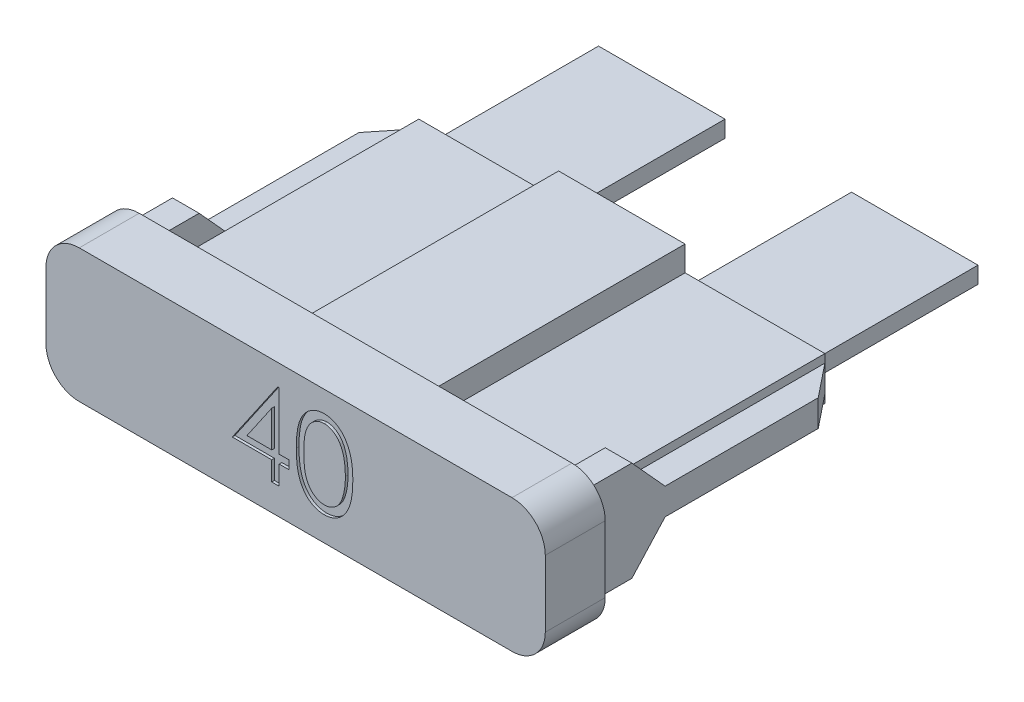
SolidWorks part; units mm, degrees
ref_plane "Front Plane" through (0, 0, 0) normal (0, 0, 1) x (1, 0, 0)
ref_plane "Top Plane" through (0, 0, 0) normal (0, 1, 0) x (1, 0, 0)
ref_plane "Right Plane" through (0, 0, 0) normal (1, 0, 0) x (0, 0, -1)
sketch "Sketch1" plane through (0, 0, 0) normal (0, 0, 1) x (1, 0, 0)
  line L1 (1.27, 0) -> (17.78, 0)
  line L2 (0, 1.27) -> (0, 3.81)
  line L3 (1.27, 5.08) -> (17.78, 5.08)
  line L4 (19.05, 1.27) -> (19.05, 3.81)
  arc A0 (0, 3.81) -> (1.27, 5.08) centre (1.27, 3.81) cw
  arc A1 (1.27, 0) -> (0, 1.27) centre (1.27, 1.27) cw
  arc A2 (19.05, 1.27) -> (17.78, 0) centre (17.78, 1.27) cw
  arc A3 (17.78, 5.08) -> (19.05, 3.81) centre (17.78, 3.81) cw
  point P8 (0, 0)
  dimension "D3" = 1.27
  dimension "D1" = 5.08
  dimension "D2" = 19.05
extrude "Extrude1" add sketch "Sketch1" along normal blind 2.286
sketch "Sketch2" plane through (0, 0, 0) normal (0, 0, -1) x (-1, 0, 0)
  line L0 (-7.62, 2.2225) -> (-7.62, 1.27)
  line L1 (-16.764, 2.8575) -> (-11.43, 2.8575)
  line L2 (-16.764, 2.8575) -> (-16.764, 2.2225)
  line L3 (-16.764, 2.2225) -> (-11.43, 2.2225)
  line L4 (-11.43, 2.2225) -> (-11.43, 1.27)
  line L5 (-11.43, 3.81) -> (-7.62, 3.81)
  line L6 (-11.43, 3.81) -> (-11.43, 2.8575)
  line L7 (-11.43, 1.27) -> (-7.62, 1.27)
  line L8 (-7.62, 3.81) -> (-7.62, 2.8575)
  line L9 (-7.62, 2.8575) -> (-2.286, 2.8575)
  line L10 (-11.938, 4.318) -> (-11.938, 3.3655)
  line L11 (-7.62, 2.2225) -> (-2.286, 2.2225)
  line L12 (-2.286, 2.8575) -> (-2.286, 2.2225)
  line L13 (-17.272, 3.3655) -> (-11.938, 3.3655)
  line L14 (-17.272, 3.3655) -> (-17.272, 1.7145)
  line L15 (-17.272, 1.7145) -> (-11.938, 1.7145)
  line L16 (-11.938, 1.7145) -> (-11.938, 0.762)
  line L17 (-11.938, 0.762) -> (-7.112, 0.762)
  line L18 (-7.112, 1.7145) -> (-7.112, 0.762)
  line L19 (-7.112, 1.7145) -> (-1.778, 1.7145)
  line L20 (-1.778, 3.3655) -> (-1.778, 1.7145)
  line L21 (-7.112, 3.3655) -> (-1.778, 3.3655)
  line L22 (-7.112, 4.318) -> (-7.112, 3.3655)
  line L23 (-11.938, 4.318) -> (-7.112, 4.318)
  line L24 (-17.78, 5.08) -> (-1.27, 5.08) construction
  line L25 (-1.27, 0) -> (-17.78, 0) construction
  line L26 (-19.05, 1.27) -> (-19.05, 3.81) construction
  line L27 (0, 3.81) -> (0, 1.27) construction
  dimension "D1" = 0.635
  dimension "D2" = 2.54
  dimension "D3" = 0.9525
  dimension "D5" = 0.762
  dimension "D6" = 0.762
  dimension "D7" = 1.778
  dimension "D8" = 14.478
  dimension "D9" = 3.81
  dimension "D10" = 5.334
  dimension "D11" = 5.334
  dimension "D12" = 1.778
  dimension "D4" = 0.508
extrude "Extrude2" add sketch "Sketch2" along normal blind 10.16
sketch "Sketch3" plane through (1.778, 0, 0) normal (-1, 0, 0) x (0, 0, 1)
  line L0 (-10.16, 1.7145) -> (-10.16, 3.3655) construction
  line L1 (-10.16, 3.048) -> (-3.048, 3.048)
  line L2 (-10.16, 3.048) -> (-10.16, 2.032)
  line L3 (-10.16, 2.032) -> (-3.048, 2.032)
  line L5 (0, 3.81) -> (0, 1.27) construction
  line L6 (-1.778, 4.445) -> (0, 4.445)
  line L8 (-1.778, 0.635) -> (0, 0.635)
  line L9 (0, 4.445) -> (0, 0.635)
  line L10 (-10.16, 3.3655) -> (0, 3.3655) construction
  line L11 (-10.16, 1.7145) -> (0, 1.7145) construction
  line L12 (-1.778, 4.445) -> (-3.048, 3.048)
  line L13 (-3.048, 2.032) -> (-1.778, 0.635)
  dimension "D1" = 1.016
  dimension "D2" = 0.3175
  dimension "D3" = 0.3175
  dimension "D4" = 3.81
  dimension "D5" = 1.397
  dimension "D6" = 1.397
  dimension "D7" = 1.27
  dimension "D8" = 1.778
extrude "Extrude3" add sketch "Sketch3" along normal blind 1.016
sketch "Sketch4" plane through (17.272, 0, 0) normal (1, 0, 0) x (0, 0, -1)
  line L0 (10.16, 3.3655) -> (10.16, 1.7145) construction
  line L1 (3.048, 3.048) -> (10.16, 3.048)
  line L3 (3.048, 2.032) -> (10.16, 2.032)
  line L4 (10.16, 3.048) -> (10.16, 2.032)
  line L5 (0, 3.81) -> (0, 5.08) construction
  line L6 (0, 4.445) -> (1.778, 4.445)
  line L7 (0, 4.445) -> (0, 0.635)
  line L8 (0, 0.635) -> (1.778, 0.635)
  line L10 (1.778, 4.445) -> (3.048, 3.048)
  line L11 (1.778, 0.635) -> (3.048, 2.032)
  line L12 (10.16, 3.3655) -> (0, 3.3655) construction
  dimension "D1" = 1.016
  dimension "D2" = 0.3175
  dimension "D3" = 1.397
  dimension "D4" = 3.81
  dimension "D5" = 1.27
  dimension "D6" = 7.112
extrude "Extrude4" add sketch "Sketch4" along normal blind 1.016
chamfer "Chamfer1" distance 1.016 distance2 1.27 2 edges at (0.762, 2.54, -10.16) (18.288, 2.54, -10.16)
sketch "Sketch8" plane through (0, 2.2225, 0) normal (0, 1, 0) x (-1, 0, 0)
  line L0 (-11.938, -10.16) -> (-11.938, 0) construction
  line L1 (-2.286, 0) -> (-7.112, 0)
  line L2 (-2.286, 0) -> (-2.286, -16.51)
  line L3 (-2.286, -16.51) -> (-7.112, -16.51)
  line L4 (-7.112, 0) -> (-7.112, -6.858)
  line L5 (-16.764, 0) -> (-11.938, 0)
  line L6 (-16.764, 0) -> (-16.764, -16.51)
  line L7 (-16.764, -16.51) -> (-11.938, -16.51)
  line L8 (-11.938, 0) -> (-11.938, -6.858)
  line L9 (-7.112, -10.16) -> (-7.112, 0) construction
  line L10 (-1.778, -10.16) -> (-7.112, -10.16) construction
  line L11 (-11.938, -10.16) -> (-17.272, -10.16) construction
  line L12 (-7.112, -7.62) -> (-8.128, -7.62)
  line L13 (-8.763, -6.985) -> (-8.763, -3.175)
  line L14 (-9.398, -2.54) -> (-9.652, -2.54)
  line L15 (-10.287, -3.175) -> (-10.287, -6.985)
  line L16 (-10.922, -7.62) -> (-11.938, -7.62)
  line L17 (-7.112, -10.16) -> (-11.938, -10.16) construction
  line L18 (-11.684, -6.858) -> (-11.938, -6.858)
  line L19 (-11.049, -3.175) -> (-11.049, -6.223)
  line L20 (-9.398, -1.778) -> (-9.652, -1.778)
  line L21 (-8.001, -6.223) -> (-8.001, -3.175)
  line L22 (-7.112, -6.858) -> (-7.366, -6.858)
  line L23 (-11.938, -7.62) -> (-11.938, -16.51)
  line L24 (-7.112, -7.62) -> (-7.112, -16.51)
  arc A0 (-9.652, -2.54) -> (-10.287, -3.175) centre (-9.652, -3.175) ccw
  arc A1 (-8.763, -3.175) -> (-9.398, -2.54) centre (-9.398, -3.175) ccw
  arc A2 (-10.922, -7.62) -> (-10.287, -6.985) centre (-10.922, -6.985) ccw
  arc A3 (-8.128, -7.62) -> (-8.763, -6.985) centre (-8.128, -6.985) cw
  arc A4 (-9.652, -1.778) -> (-11.049, -3.175) centre (-9.652, -3.175) ccw
  arc A5 (-8.001, -3.175) -> (-9.398, -1.778) centre (-9.398, -3.175) ccw
  arc A6 (-7.366, -6.858) -> (-8.001, -6.223) centre (-7.366, -6.223) cw
  arc A7 (-11.684, -6.858) -> (-11.049, -6.223) centre (-11.684, -6.223) ccw
  point P26 (-10.287, -2.54)
  point P29 (-8.763, -2.54)
  point P32 (-10.287, -7.62)
  point P35 (-8.763, -7.62)
  dimension "D6" = 0.635
  dimension "D8" = 0.635
  dimension "D1" = 6.35
  dimension "D2" = 6.35
  dimension "D3" = 1.524
  dimension "D4" = 5.08
  dimension "D5" = 2.54
  dimension "D7" = 0.762
extrude "Blade" add sketch "Sketch8" along normal up to surface (0.635 mm away) up to face at (4.953, 2.8575, -5.08)
sketch "Sketch5" plane through (0, 0, 2.286) normal (0, 0, 1) x (1, 0, 0)
  line L0 (0, 3.81) -> (0, 1.27) construction
  line L1 (1.27, 0) -> (17.78, 0) construction
  text T0 "10" font "Century Gothic" height in points 12
  dimension "D1" = 6.7818
  dimension "D2" = 0.9525
extrude "\"10\"" [suppressed] cut sketch "Sketch5" against normal blind 0.1016
sketch "Sketch6" plane through (0, 0, 2.286) normal (0, 0, 1) x (1, 0, 0)
  line L0 (1.27, 0) -> (17.78, 0) construction
  line L1 (0, 3.81) -> (0, 1.27) construction
  text T0 "40" font "Century Gothic" height in points 12
  dimension "D1" = 1.016
  dimension "D2" = 6.985
extrude "\"40\"" cut sketch "Sketch6" against normal blind 0.1016
sketch "Sketch7" [suppressed] plane through (0, 0, 2.286) normal (0, 0, 1) x (1, 0, 0)
  line L0 (1.27, 0) -> (17.78, 0) construction
  line L1 (0, 3.81) -> (0, 1.27) construction
  text T0 "30" font "Century Gothic" height in points 12
  dimension "D1" = 1.016
  dimension "D2" = 6.985
extrude "\"30\"" [suppressed] cut sketch "Sketch7" against normal blind 0.1016
sketch "Sketch9" [suppressed] plane through (0, 0, 2.286) normal (0, 0, 1) x (1, 0, 0)
  line L0 (1.27, 0) -> (17.78, 0) construction
  line L1 (0, 3.81) -> (0, 1.27) construction
  text T0 "7.5" font "Century Gothic" height in points 12
  dimension "D1" = 1.016
  dimension "D2" = 6.604
extrude "\"7.5\"" [suppressed] cut sketch "Sketch9" against normal blind 0.1016
sketch "Sketch10" [suppressed] plane through (0, 0, 2.286) normal (0, 0, 1) x (1, 0, 0)
  line L0 (1.27, 0) -> (17.78, 0) construction
  line L1 (0, 3.81) -> (0, 1.27) construction
  text T0 "1" font "Century Gothic" height in points 12
  dimension "D1" = 1.016
  dimension "D2" = 8.255
extrude "\"1\"" [suppressed] cut sketch "Sketch10" against normal blind 0.1016
sketch "Sketch11" [suppressed] plane through (0, 0, 2.286) normal (0, 0, 1) x (1, 0, 0)
  line L0 (1.27, 0) -> (17.78, 0) construction
  line L1 (0, 3.81) -> (0, 1.27) construction
  text T0 "15" font "Century Gothic" height in points 12
  dimension "D1" = 1.016
  dimension "D2" = 6.858
extrude "\"15\"" [suppressed] cut sketch "Sketch11" against normal blind 0.1016
sketch "Sketch12" [suppressed] plane through (0, 0, 2.286) normal (0, 0, 1) x (1, 0, 0)
  line L0 (1.27, 0) -> (17.78, 0) construction
  line L1 (0, 3.81) -> (0, 1.27) construction
  text T0 "2" font "Century Gothic" height in points 12
  dimension "D1" = 1.016
  dimension "D2" = 8.255
extrude "\"2\"" [suppressed] cut sketch "Sketch12" against normal blind 0.1016
sketch "Sketch13" [suppressed] plane through (0, 0, 2.286) normal (0, 0, 1) x (1, 0, 0)
  line L0 (1.27, 0) -> (17.78, 0) construction
  line L1 (0, 3.81) -> (0, 1.27) construction
  text T0 "20" font "Century Gothic" height in points 12
  dimension "D1" = 1.016
  dimension "D2" = 6.985
extrude "\"20\"" [suppressed] cut sketch "Sketch13" against normal blind 0.1016
sketch "Sketch14" [suppressed] plane through (0, 0, 2.286) normal (0, 0, 1) x (1, 0, 0)
  line L0 (1.27, 0) -> (17.78, 0) construction
  line L1 (0, 3.81) -> (0, 1.27) construction
  text T0 "25" font "Century Gothic" height in points 12
  dimension "D1" = 1.016
  dimension "D2" = 6.985
extrude "\"25\"" [suppressed] cut sketch "Sketch14" against normal blind 0.1016
sketch "Sketch15" [suppressed] plane through (0, 0, 2.286) normal (0, 0, 1) x (1, 0, 0)
  line L0 (1.27, 0) -> (17.78, 0) construction
  line L1 (0, 3.81) -> (0, 1.27) construction
  text T0 "3" font "Century Gothic" height in points 12
  dimension "D1" = 1.016
  dimension "D2" = 8.255
extrude "\"3\"" [suppressed] cut sketch "Sketch15" against normal blind 0.1016
sketch "Sketch16" [suppressed] plane through (0, 0, 2.286) normal (0, 0, 1) x (1, 0, 0)
  line L0 (1.27, 0) -> (17.78, 0) construction
  line L1 (0, 3.81) -> (0, 1.27) construction
  text T0 "4" font "Century Gothic" height in points 12
  dimension "D1" = 1.016
  dimension "D2" = 8.255
extrude "\"4\"" [suppressed] cut sketch "Sketch16" against normal blind 0.1016
sketch "Sketch17" [suppressed] plane through (0, 0, 2.286) normal (0, 0, 1) x (1, 0, 0)
  line L0 (1.27, 0) -> (17.78, 0) construction
  line L1 (0, 3.81) -> (0, 1.27) construction
  text T0 "5" font "Century Gothic" height in points 12
  dimension "D1" = 1.016
  dimension "D2" = 8.255
extrude "\"5\"" [suppressed] cut sketch "Sketch17" against normal blind 0.1016
sketch3d "3DSketch1" [suppressed]
  line L0 (1.27, 0, 2.286) -> (17.78, 0, 2.286) construction
  point P0 (9.525, 0, 2.286)
ref_plane "Plane1" [suppressed] through (9.525, 0, 0) normal (1, 0, 0) x (0, 0, -1)
sketch3d "3DSketch2"
  line L0 (16.764, 2.8575, -16.51) -> (11.938, 2.2225, -16.51) construction
  line L1 (7.112, 2.8575, -16.51) -> (2.286, 2.2225, -16.51) construction
  line L2 (4.699, 2.54, -16.51) -> (4.699, 2.54, -10.3726) construction
  line L3 (14.351, 2.54, -16.51) -> (14.351, 2.54, -10.2814) construction
